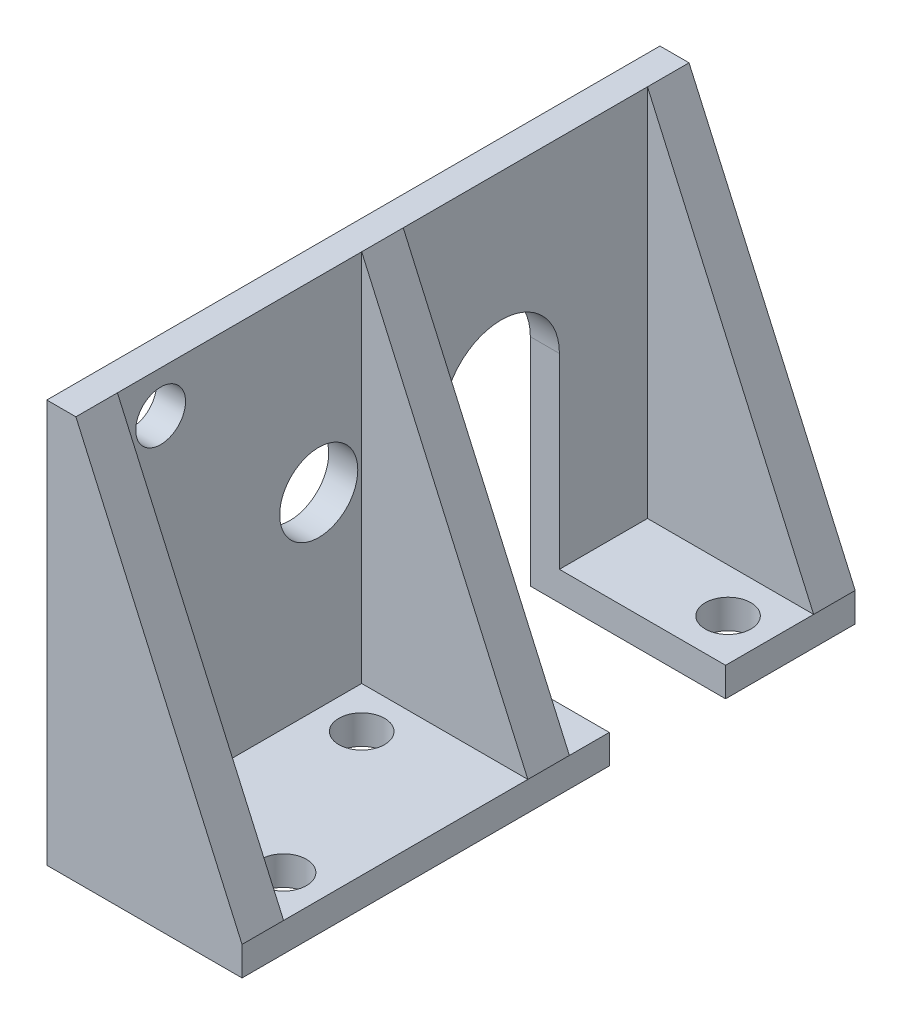
SolidWorks part; units mm, degrees
ref_plane "Front" through (0, 0, 0) normal (0, 0, 1) x (1, 0, 0)
ref_plane "Top" through (0, 0, 0) normal (0, 1, 0) x (1, 0, 0)
ref_plane "Right" through (0, 0, 0) normal (1, 0, 0) x (0, 0, -1)
sketch "Sketch1" plane through (0, 0, 0) normal (1, 0, 0) x (0, 0, -1)
  line L1 (0, 0) -> (36.9, 0)
  line L2 (0, 0) -> (0, 22.5)
  line L3 (0, 22.5) -> (36.9, 22.5)
  line L4 (36.9, 0) -> (36.9, 22.5)
  dimension "D1" = 36.9
  dimension "D2" = 22.5
extrude "basePlate" add sketch "Sketch1" along normal blind 1.75
sketch "Sketch2" plane through (0, 0, 0) normal (0, -1, 0) x (1, 0, 0)
  line L0 (1.75, -36.9) -> (0, -36.9) construction
  line L1 (0, 0) -> (11.75, 0)
  line L2 (0, 0) -> (0, -36.9)
  line L3 (0, -36.9) -> (11.75, -36.9)
  line L4 (11.75, 0) -> (11.75, -36.9)
  dimension "D1" = 11.75
extrude "Boss-Extrude2" add sketch "Sketch2" along normal blind 1.75
sketch "Sketch3" plane through (0, 0, 0) normal (0, 0, 1) x (1, 0, 0)
  line L0 (1.75, 22.5) -> (11.75, 0)
rib "support1" sketch "Sketch3" sketch "Sketch3" thickness 2.5 extrusion direction parallel to sketch draft on no parameters "D1"=2.5
ref_plane "referencePlane" through (0, 0, -18.45) normal (0, 0, 1) x (1, 0, 0)
mirror "support2" about plane through (0, 0, -18.45) normal (0, 0, 1) of "support1"
sketch "Sketch4" plane through (0, 0, -18.45) normal (0, 0, 1) x (1, 0, 0)
  line L0 (1.75, 22.5) -> (11.75, 0)
rib "support3" sketch "Sketch4" sketch "Sketch4" thickness 2.5 extrusion direction parallel to sketch draft on no parameters "D1"=2.5
sketch "Sketch5" plane through (1.75, 0, 0) normal (1, 0, 0) x (0, 0, -1)
  line L1 (17.2, 22.5) -> (2.5, 22.5) construction
  circle A0 centre (5.1, 2.5) radius 1.5
  circle A1 centre (5.1, 20) radius 1.5
  dimension "D1" = 3
  dimension "D2" = 17.5
  dimension "D3" = 2.5
  dimension "D4" = 31.8
extrude "motor_mountingHoles" cut sketch "Sketch5" against normal through all
sketch "Sketch7" plane through (11.75, 0, 0) normal (1, 0, 0) x (0, 0, -1)
  line L0 (25.6, 22.5) -> (25.6, 0) construction
  line L1 (34.4, 22.5) -> (19.7, 22.5) construction
  line L2 (19.7, 0) -> (34.4, 0) construction
  line L4 (22.1, -1.75) -> (22.1, 11.25)
  line L5 (36.9, -1.75) -> (0, -1.75) construction
  line L6 (29.1, -1.75) -> (29.1, 11.25)
  line L7 (22.1, -1.75) -> (29.1, -1.75)
  line L8 (0, -1.75) -> (0, 0) construction
  arc A0 (29.1, 11.25) -> (22.1, 11.25) centre (25.6, 11.25) ccw
  dimension "D1" = 7
  dimension "D2" = 25.6
extrude "shaftSlot" cut sketch "Sketch7" against normal through all
sketch "Sketch8" plane through (0, 0, 0) normal (0, 1, 0) x (1, 0, 0)
  line L0 (11.75, 2.5) -> (1.75, 2.5) construction
  line L1 (11.75, 17.2) -> (11.75, 2.5) construction
  line L3 (1.75, 2.5) -> (1.75, 17.2) construction
  line L4 (9.25, 29.1) -> (9.25, 34.4) construction
  line L5 (1.75, 29.1) -> (11.75, 29.1) construction
  line L6 (1.75, 34.4) -> (11.75, 34.4) construction
  line L7 (4.25, 29.1) -> (4.25, 34.4) construction
  line L8 (11.75, 34.4) -> (11.75, 29.1) construction
  line L9 (1.75, 29.1) -> (1.75, 34.4) construction
  line L10 (11.75, 17.2) -> (1.75, 17.2) construction
  circle A0 centre (9.25, 5) radius 1.375
  circle A2 centre (4.25, 14.7) radius 1.375
  circle A4 centre (9.25, 31.75) radius 1.375
  dimension "D1" = 2.75
  dimension "D2" = 2.5
  dimension "D3" = 2.5
  dimension "D4" = 2.5
  dimension "D5" = 2.5
  dimension "D6" = 2.5
  dimension "D7" = 2.5
extrude "chassis_mountingHoles" cut sketch "Sketch8" against normal through all
sketch "Sketch9" plane through (1.75, 0, 0) normal (1, 0, 0) x (0, 0, -1)
  line L0 (22.1, 11.25) -> (29.1, 11.25) construction
  circle A0 centre (14.615, 11.25) radius 2.35
  point P6 (25.6, 11.25)
  dimension "D1" = 4.7
  dimension "D2" = 10.985
extrude "indentHole" cut sketch "Sketch9" against normal blind 10
